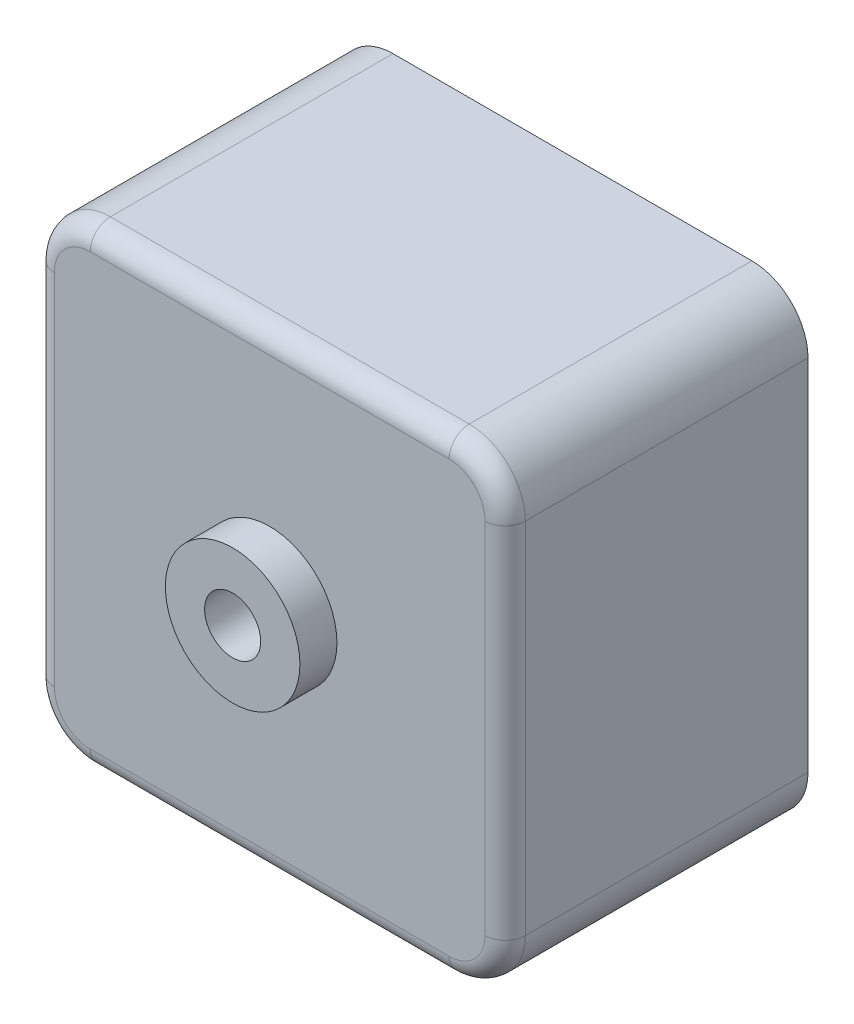
SolidWorks part; units mm, degrees
ref_plane "Alzado" through (0, 0, 0) normal (0, 0, 1) x (1, 0, 0)
ref_plane "Planta" through (0, 0, 0) normal (0, 1, 0) x (1, 0, 0)
ref_plane "Vista lateral" through (0, 0, 0) normal (1, 0, 0) x (0, 0, -1)
ref_plane "Plano1" through (0, 0, 27) normal (0, 0, 1) x (1, 0, 0)
sketch "Croquis1" plane through (0, 0, 27) normal (0, 0, 1) x (1, 0, 0)
  line L0 (42, 42) -> (0, 42)
  line L1 (0, 42) -> (0, 0)
  line L2 (0, 0) -> (42, 0)
  line L3 (42, 0) -> (42, 42)
extrude "Saliente-Extruir1" add sketch "Croquis1" against normal blind 27
ref_plane "Plano2" through (0, 21, 0) normal (0, 1, 0) x (1, 0, 0)
sketch "Croquis2" plane through (0, 21, 0) normal (0, 1, 0) x (1, 0, 0)
  line L0 (27, -27) -> (21, -27)
  line L1 (21, -27) -> (21, -37.8)
  line L2 (21, -37.8) -> (23.5, -37.8)
  line L3 (23.5, -37.8) -> (23.5, -30.3)
  line L4 (23.5, -30.3) -> (27, -30.3)
  line L5 (27, -30.3) -> (27, -27)
  line L6 (21, -27) -> (21, -37.8) construction
revolve "Revolución1" add sketch "Croquis2" angle 360 about L6
fillet "Redondeo1" radius 5 4 edges at (42, 0, 13.5) (0, 42, 13.5) (0, 0, 13.5) (42, 42, 13.5)
fillet "Redondeo2" radius 1.8 8 edges at (40.5355, 1.4645, 27) (21, 0, 27) (42, 21, 27) (1.4645, 1.4645, 27) (40.5355, 40.5355, 27) (0, 21, 27) (21, 42, 27) (1.4645, 40.5355, 27)
ref_plane "Plano3" through (0, 0, 37.8) normal (0, 0, 1) x (1, 0, 0)
sketch "Croquis4" plane through (0, 0, 37.8) normal (0, 0, 1) x (1, 0, 0)
  circle A0 centre (21, 21) radius 2.5
extrude "Cortar-Extruir1" cut sketch "Croquis4" against normal through all
